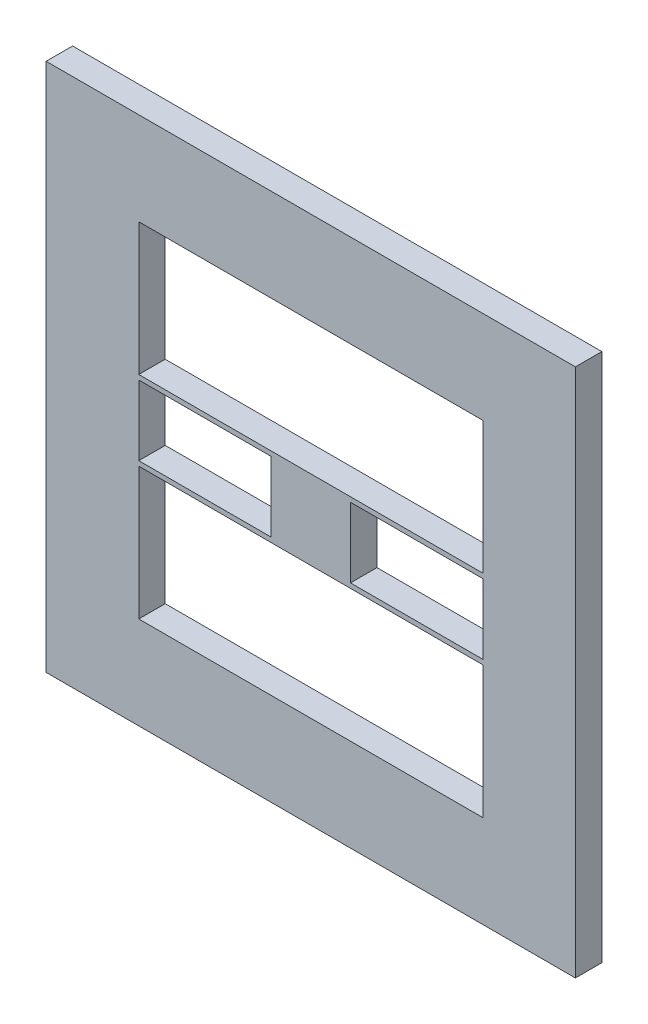
SolidWorks part; units mm, degrees
ref_plane "Front" through (0, 0, 0) normal (0, 0, 1) x (1, 0, 0)
ref_plane "Top" through (0, 0, 0) normal (0, 1, 0) x (1, 0, 0)
ref_plane "Right" through (0, 0, 0) normal (1, 0, 0) x (0, 0, -1)
sketch "Sketch1" plane through (0, 0, 0) normal (0, 0, 1) x (1, 0, 0)
  line L0 (0.075, 0.075) -> (-0.075, -0.075) construction
  line L1 (-0.075, 0.075) -> (0.075, 0.075)
  line L2 (-0.075, 0.075) -> (-0.075, -0.075)
  line L3 (-0.075, -0.075) -> (0.075, -0.075)
  line L4 (0.075, 0.075) -> (0.075, -0.075)
  dimension "D1" = 0.15
extrude "Extrude1" add sketch "Sketch1" along normal blind 0.05
sketch "Sketch2" plane through (0, 0, 0.05) normal (0, 0, 1) x (1, 0, 0)
  line L0 (-0.075, 0) -> (0.075, 0) construction
  line L1 (0.075, 0.075) -> (0.325, 0.075)
  line L2 (0.075, 0.075) -> (0.075, 0.066)
  line L3 (0.075, 0.066) -> (0.325, 0.066)
  line L4 (0.325, 0.075) -> (0.325, 0.066)
  line L5 (-0.075, 0.075) -> (-0.075, -0.075) construction
  line L6 (0.075, -0.075) -> (0.075, 0.075) construction
  line L7 (0, 0.075) -> (0, -0.075) construction
  line L8 (0.075, 0.075) -> (-0.075, 0.075) construction
  line L9 (-0.075, -0.075) -> (0.075, -0.075) construction
  line L10 (-0.325, 0.075) -> (-0.325, 0.066)
  line L11 (-0.075, 0.066) -> (-0.325, 0.066)
  line L12 (-0.075, 0.075) -> (-0.075, 0.066)
  line L13 (-0.075, 0.075) -> (-0.325, 0.075)
  line L14 (-0.075, -0.075) -> (-0.325, -0.075)
  line L15 (-0.075, -0.075) -> (-0.075, -0.066)
  line L16 (-0.075, -0.066) -> (-0.325, -0.066)
  line L17 (-0.325, -0.075) -> (-0.325, -0.066)
  line L18 (0.325, -0.075) -> (0.325, -0.066)
  line L19 (0.075, -0.066) -> (0.325, -0.066)
  line L20 (0.075, -0.075) -> (0.075, -0.066)
  line L21 (0.075, -0.075) -> (0.325, -0.075)
  dimension "D1" = 0.25
  dimension "D2" = 0.009
extrude "Extrude2" add sketch "Sketch2" against normal up to surface (0.05 mm away) up to face at (0, 0, 0)
sketch "Sketch3" plane through (0, 0, 0.05) normal (0, 0, 1) x (1, 0, 0)
  line L0 (0.325, -0.075) -> (0.325, -0.066) construction
  line L1 (-0.5, 0.5) -> (0.5, 0.5)
  line L2 (-0.5, 0.5) -> (-0.5, -0.5)
  line L3 (-0.5, -0.5) -> (0.5, -0.5)
  line L4 (0.5, 0.5) -> (0.5, -0.5)
  line L5 (-0.325, 0.325) -> (0.325, 0.325)
  line L6 (-0.325, 0.325) -> (-0.325, -0.325)
  line L7 (-0.325, -0.325) -> (0.325, -0.325)
  line L8 (0.325, 0.325) -> (0.325, -0.325)
  line L9 (-0.325, 0.075) -> (-0.325, 0.066) construction
  line L10 (0.325, 0.075) -> (-0.325, 0.075) construction
  line L11 (-0.075, 0) -> (0.075, 0) construction
  line L12 (-0.075, 0.066) -> (-0.075, -0.066) construction
  line L13 (0.075, -0.066) -> (0.075, 0.066) construction
  line L14 (0, -0.075) -> (0, 0.075) construction
  line L15 (-0.325, -0.075) -> (0.325, -0.075) construction
  line L16 (0.325, 0.325) -> (0.5, 0.325) construction
  line L17 (0.325, 0.325) -> (0.325, 0.5) construction
  dimension "D1" = 1
  dimension "D2" = 1
extrude "Extrude3" add sketch "Sketch3" against normal up to surface (0.05 mm away) up to face at (0, 0, 0)
